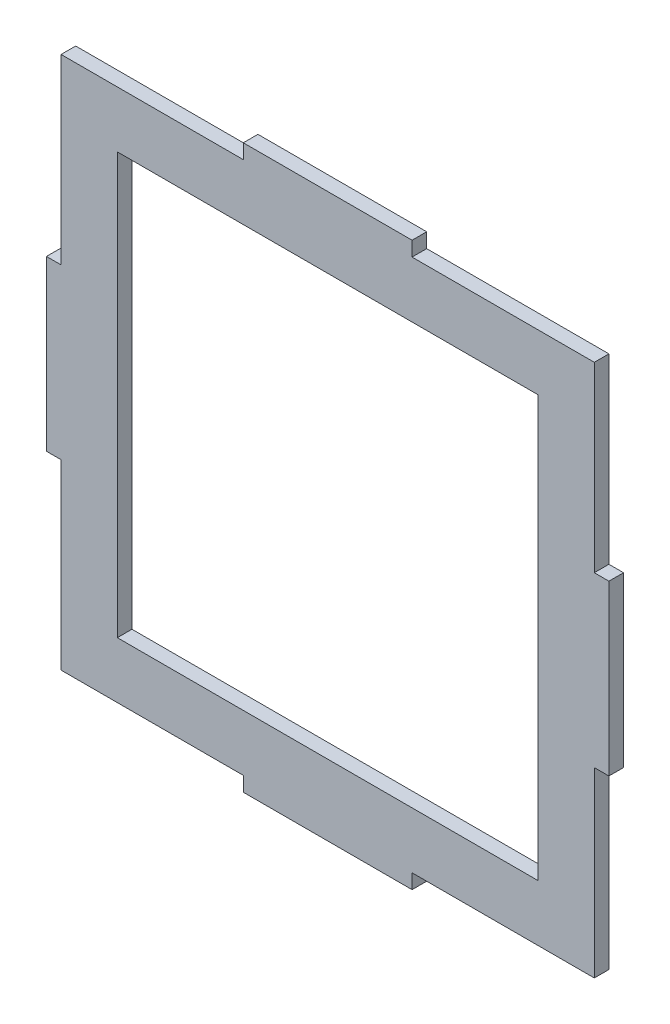
SolidWorks part; units mm, degrees
ref_plane "Front Plane" through (0, 0, 0) normal (0, 0, 1) x (1, 0, 0)
ref_plane "Top Plane" through (0, 0, 0) normal (0, 1, 0) x (1, 0, 0)
ref_plane "Right Plane" through (0, 0, 0) normal (1, 0, 0) x (0, 0, -1)
sketch "Sketch3" plane through (0, 0, 0) normal (0, 0, 1) x (1, 0, 0)
  line L0 (62.4, 94.8) -> (94.8, 94.8)
  line L1 (0, 0) -> (32.4, 0)
  line L2 (0, 0) -> (0, 32.4)
  line L3 (0, 94.8) -> (32.4, 94.8)
  line L4 (94.8, 0) -> (94.8, 32.4)
  line L5 (94.8, 62.4) -> (94.8, 94.8)
  line L6 (32.4, 94.8) -> (32.4, 97.4)
  line L7 (32.4, 97.4) -> (62.4, 97.4)
  line L8 (62.4, 94.8) -> (62.4, 97.4)
  line L9 (94.8, 62.4) -> (97.4, 62.4)
  line L10 (0, 62.4) -> (0, 94.8)
  line L11 (94.8, 32.4) -> (97.4, 32.4)
  line L12 (97.4, 62.4) -> (97.4, 32.4)
  line L14 (62.4, 0) -> (62.4, -2.6)
  line L15 (62.4, -2.6) -> (32.4, -2.6)
  line L16 (32.4, 0) -> (32.4, -2.6)
  line L17 (0, 62.4) -> (-2.6, 62.4)
  line L18 (62.4, 0) -> (94.8, 0)
  line L19 (0, 32.4) -> (-2.6, 32.4)
  line L20 (-2.6, 62.4) -> (-2.6, 32.4)
  dimension "D1" = 2.6
  dimension "D2" = 94.8
  dimension "D3" = 30
extrude "Boss-Extrude2" add sketch "Sketch3" along normal blind 2.6
sketch "Sketch4" plane through (0, 0, 2.6) normal (0, 0, 1) x (1, 0, 0)
  line L0 (16.2, 94.8) -> (16.2, 84.8) construction
  line L1 (10, 10) -> (84.8, 10)
  line L2 (10, 10) -> (10, 84.8)
  line L3 (10, 84.8) -> (84.8, 84.8)
  line L4 (84.8, 10) -> (84.8, 84.8)
  line L5 (32.4, 94.8) -> (0, 94.8) construction
  line L6 (0, 78.6) -> (10, 78.6) construction
  line L7 (0, 94.8) -> (0, 62.4) construction
  line L8 (19.9291, 0) -> (19.9291, 10) construction
  line L9 (0, 0) -> (32.4, 0) construction
  line L10 (84.8, 22.9589) -> (94.8, 22.9589) construction
  line L11 (94.8, 0) -> (94.8, 32.4) construction
  dimension "D1" = 10
extrude "Cut-Extrude1" cut sketch "Sketch4" against normal through all
equation "\"mdf\"=\"mdf@fmv1.assembly\""
equation "\"D1@Sketch3\" = \"mdf\""
equation "\"D2@Sketch3\" = 100-2*\"mdf\""
equation "\"D1@Boss-Extrude2\"=\"mdf\""
equation "\"D1@Sketch4\" = 10"
